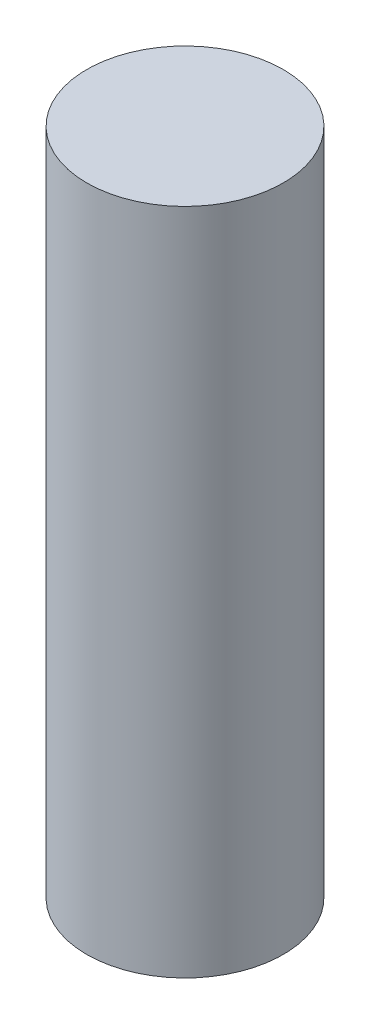
SolidWorks part; units mm, degrees
ref_plane "Front Plane" through (0, 0, 0) normal (0, 0, 1) x (1, 0, 0)
ref_plane "Top Plane" through (0, 0, 0) normal (0, 1, 0) x (1, 0, 0)
ref_plane "Right Plane" through (0, 0, 0) normal (1, 0, 0) x (0, 0, -1)
sketch "Sketch1" plane through (0, 0, 0) normal (0, 1, 0) x (1, 0, 0)
  circle A0 centre (0, 0) radius 12.5
  dimension "D1" = 25
extrude "Boss-Extrude1" add sketch "Sketch1" along normal blind 85
